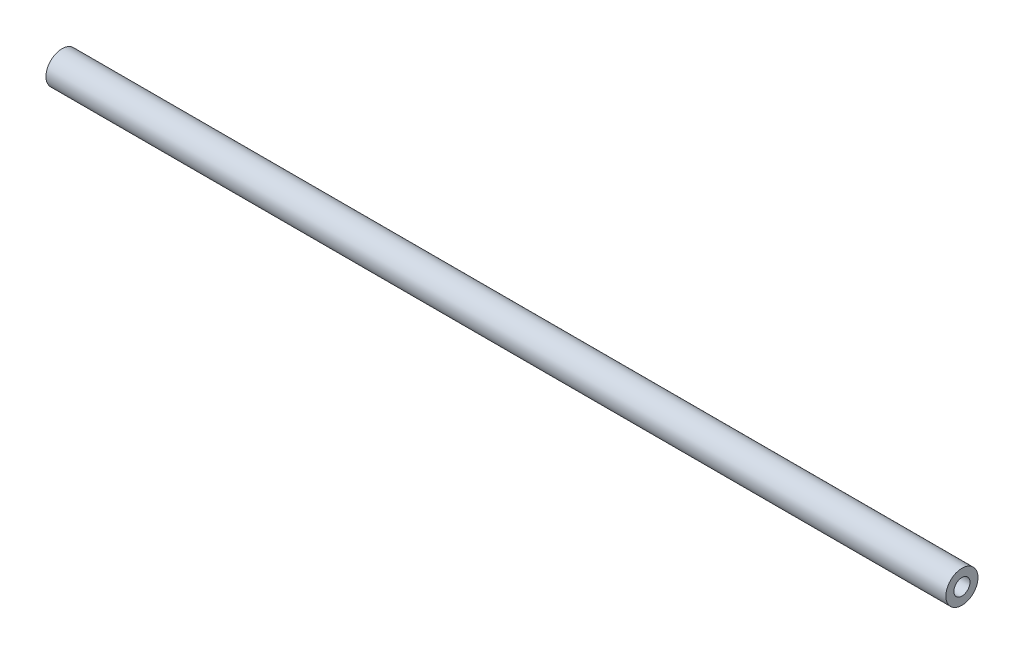
SolidWorks part; units mm, degrees
ref_plane "Front" through (0, 0, 0) normal (0, 0, 1) x (1, 0, 0)
ref_plane "Top" through (0, 0, 0) normal (0, 1, 0) x (1, 0, 0)
ref_plane "Right" through (0, 0, 0) normal (1, 0, 0) x (0, 0, -1)
sketch "Sketch1" plane through (0, 0, 0) normal (1, 0, 0) x (0, 0, -1)
  circle A0 centre (0, 0) radius 6.35
  circle A1 centre (0, 0) radius 3.175
  dimension "D1" = 12.7
  dimension "D2" = 6.35
extrude "Boss-Extrude1" add sketch "Sketch1" along normal blind 355.6
